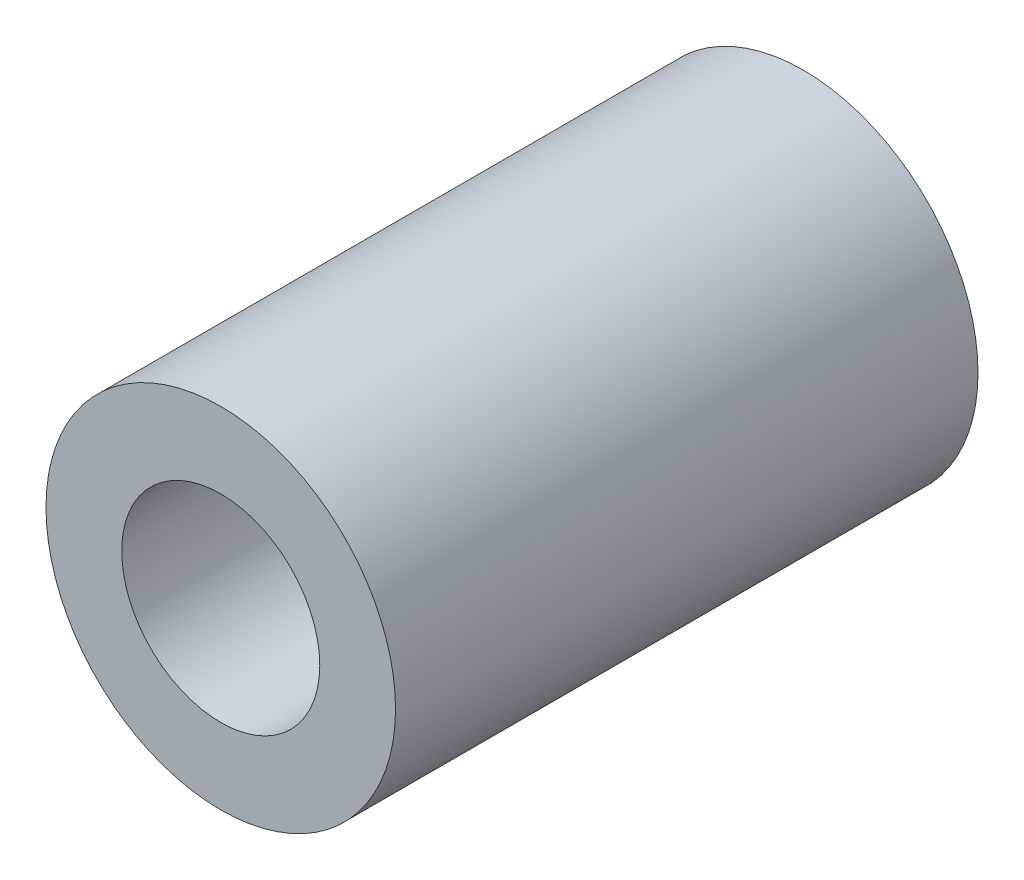
SolidWorks part; units mm, degrees
ref_plane "Front Plane" through (0, 0, 0) normal (0, 0, 1) x (1, 0, 0)
ref_plane "Top Plane" through (0, 0, 0) normal (0, 1, 0) x (1, 0, 0)
ref_plane "Right Plane" through (0, 0, 0) normal (1, 0, 0) x (0, 0, -1)
sketch "Sketch9" plane through (0, 0, 0) normal (0, 0, 1) x (1, 0, 0)
  circle A0 centre (-11.9027, 30.0594) radius 3
  dimension "D1" = 6
extrude "Boss-Extrude3" add sketch "Sketch9" along normal blind 10 contours A0
sketch "Sketch12" plane through (0, 0, 10) normal (0, 0, 1) x (1, 0, 0)
  circle A0 centre (-11.9027, 30.0594) radius 1.7
  dimension "D1" = 3.4
extrude "Cut-Extrude2" cut sketch "Sketch12" against normal through all contours A0
